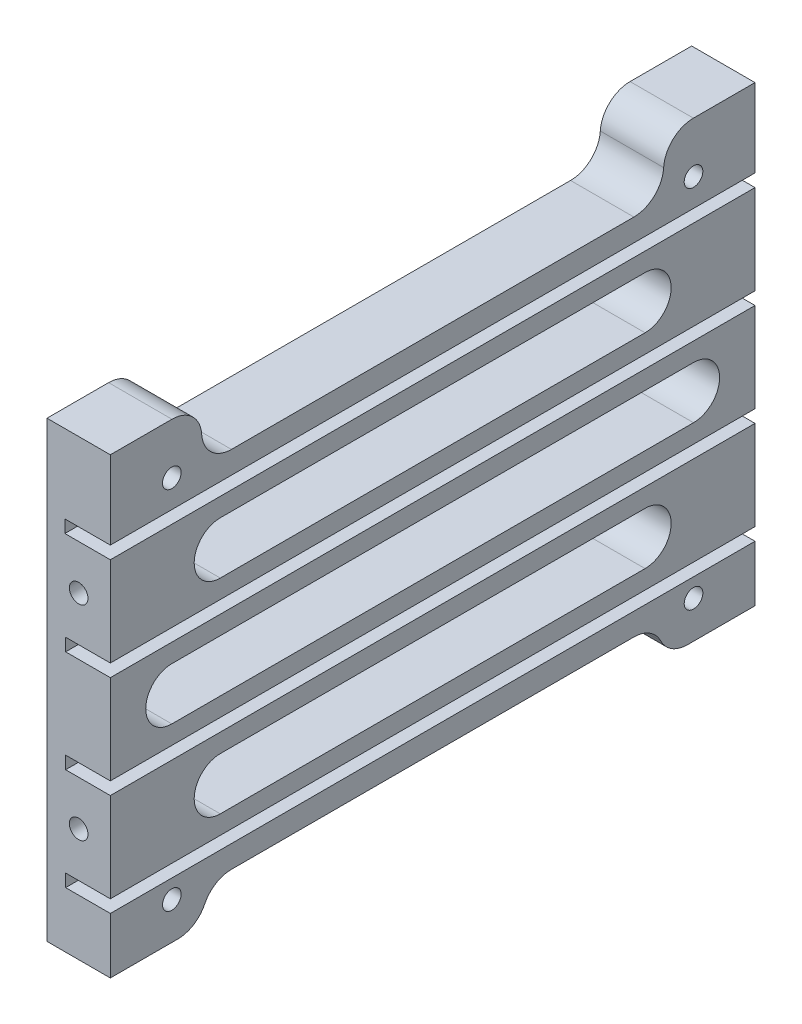
SolidWorks part; units mm, degrees
material "6061-T6 (SS)"
ref_plane "Front Plane" through (0, 0, 0) normal (0, 0, 1) x (1, 0, 0)
ref_plane "Top Plane" through (0, 0, 0) normal (0, 1, 0) x (1, 0, 0)
ref_plane "Right Plane" through (0, 0, 0) normal (1, 0, 0) x (0, 0, -1)
sketch "Sketch1" plane through (0, 0, 0) normal (0, 0, 1) x (1, 0, 0)
  line L0 (0, 0) -> (0, 60.8)
  line L1 (0, 60.8) -> (8.5, 60.8)
  line L2 (8.5, 60.8) -> (8.5, 50.3)
  line L3 (8.5, 50.3) -> (2.4, 50.3)
  line L4 (2.4, 50.3) -> (2.4, 48.6)
  line L5 (2.4, 48.6) -> (8.5, 48.6)
  line L6 (8.5, 48.6) -> (8.5, 36.6)
  line L7 (8.5, 36.6) -> (2.5, 36.6)
  line L8 (2.5, 36.6) -> (2.5, 34.9)
  line L9 (2.5, 34.9) -> (8.5, 34.9)
  line L10 (8.5, 34.9) -> (8.5, 22.9)
  line L11 (8.5, 22.9) -> (2.5, 22.9)
  line L12 (2.5, 22.9) -> (2.5, 21.2)
  line L13 (2.5, 21.2) -> (8.5, 21.2)
  line L14 (8.5, 21.2) -> (8.5, 9.2)
  line L15 (8.5, 9.2) -> (2.5, 9.2)
  line L16 (2.5, 9.2) -> (2.5, 7.5)
  line L17 (2.5, 7.5) -> (8.5, 7.5)
  line L18 (8.5, 7.5) -> (8.5, 0)
  line L19 (8.5, 0) -> (0, 0)
  dimension "D1" = 60.8
  dimension "D2" = 8.5
  dimension "D3" = 10.5
  dimension "D4" = 1.7
  dimension "D5" = 6.1
  dimension "D6" = 12
  dimension "D7" = 1.7
  dimension "D8" = 12
  dimension "D9" = 12
  dimension "D10" = 1.7
  dimension "D11" = 1.7
  dimension "D12" = 2.5
  dimension "D13" = 2.5
  dimension "D14" = 2.5
  dimension "D15" = 8.5
  dimension "D16" = 8.5
  dimension "D17" = 8.5
  dimension "D18" = 8.5
extrude "Boss-Extrude1" add sketch "Sketch1" along normal blind 86.5
sketch "Sketch2" plane through (0, 0, 86.5) normal (0, 0, 1) x (1, 0, 0)
  line L0 (8.5, 36.6) -> (8.5, 48.6) construction
  line L3 (8.5, 48.6) -> (2.4, 48.6) construction
  line L4 (8.5, 21.2) -> (2.5, 21.2) construction
  line L8 (8.5, 9.2) -> (8.5, 21.2) construction
  point P0 (4.25, 15.2)
  point P11 (4.25, 42.6)
  dimension "D1" = 4.25
  dimension "D2" = 6
  dimension "D3" = 4.25
  dimension "D4" = 6
hole_wizard "M3x0.5 Tapped Hole2" positions "Sketch3" profile "Sketch4" tap size "M3x0.5" standard "ANSI Metric"
sketch "Sketch3" plane through (0, 0, 86.5) normal (0, 0, 1) x (1, 0, 0)
  point P0 (4.25, 42.6)
  point P3 (4.25, 15.2)
sketch "Sketch4" plane through (4.25, 42.6, 86.5) normal (1, 0, 0) x (0, -1, 0)
  line L0 (0, 0) -> (0, 6.7511)
  line L1 (0, 6.7511) -> (1.25, 6)
  line L2 (1.25, 6) -> (1.25, 0)
  line L5 (1.25, 0) -> (0, 0)
  line L10 (0, 6.7511) -> (-1.25, 6) construction
  line L11 (0, -6.35) -> (0, 107.95) construction
  dimension "Tap Drill Dia." = 2.5
  dimension "Tap Drill Depth" = 6
  dimension "Drill Angle" = 118
ref_plane "Plane1" through (0, 0, 43.25) normal (0, 0, 1) x (1, 0, 0)
mirror "Mirror1" about plane through (0, 0, 43.25) normal (0, 0, 1) of "M3x0.5 Tapped Hole2"
sketch "Sketch5" plane through (0, 0, 0) normal (-1, 0, 0) x (0, 0, 1)
  line L1 (86.5, 60.8) -> (0, 60.8) construction
  line L5 (0, 60.8) -> (0, 0) construction
  line L7 (86.5, 0) -> (0, 0) construction
  line L8 (86.5, 60.8) -> (86.5, 0) construction
  point P0 (78.25, 5)
  point P3 (8.25, 5)
  point P4 (8.25, 55.8)
  point P7 (78.25, 55.8)
  dimension "D1" = 5
  dimension "D2" = 8.25
  dimension "D3" = 70
  dimension "D4" = 5
  dimension "D5" = 5
  dimension "D6" = 8.25
  dimension "D7" = 8.25
  dimension "D8" = 5
hole_wizard "M3x0.5 Tapped Hole1" positions "Sketch10" profile "Sketch11" tap size "M3x0.5" standard "ANSI Metric" end condition through all
sketch "Sketch10" plane through (0, 0, 0) normal (-1, 0, 0) x (0, 0, 1)
  line L0 (43.25, 60.8) -> (43.25, 0) construction
  line L1 (86.5, 60.8) -> (0, 60.8) construction
  line L2 (86.5, 0) -> (0, 0) construction
  line L7 (43.25, 54) -> (8.25, 54) construction
  line L12 (43.25, 5) -> (8.25, 5) construction
  point P16 (8.25, 54)
  point P26 (8.25, 5)
  dimension "D1" = 49
sketch "Sketch11" plane through (0, 5, 8.25) normal (0, 1, 0) x (0, 0, 1)
  line L0 (0, 0) -> (0, 8.5)
  line L1 (0, 8.5) -> (1.25, 8.5)
  line L2 (1.25, 8.5) -> (1.25, 0)
  line L5 (1.25, 0) -> (0, 0)
  line L11 (0, -6.35) -> (0, 107.95) construction
  dimension "Thru Tap Drill Dia." = 2.5
  dimension "Thru Tap Drill Depth" = 8.5
ref_plane "Plane2" through (0, 0, 43.25) normal (0, 0, -1) x (-1, 0, 0)
mirror "Mirror2" about plane through (0, 0, 43.25) normal (0, 0, -1) of "M3x0.5 Tapped Hole1"
sketch "Sketch14" plane through (8.5, 0, 0) normal (1, 0, 0) x (0, 0, -1)
  line L0 (-43.25, 60.8) -> (-43.25, 0) construction
  line L1 (-86.5, 60.8) -> (0, 60.8) construction
  line L2 (-86.5, 0) -> (0, 0) construction
  line L3 (-86.5, 28.9) -> (0, 28.9) construction
  line L4 (-86.5, 22.9) -> (-86.5, 34.9) construction
  line L5 (0, 22.9) -> (0, 34.9) construction
  line L6 (-78.25, 32.4) -> (-8.25, 32.4)
  line L7 (-8.25, 25.4) -> (-78.25, 25.4)
  circle A0 centre (-78.25, 28.9) radius 3.5
  circle A1 centre (-8.25, 28.9) radius 3.5
  dimension "D1" = 7
  dimension "D2" = 35
extrude "Cut-Extrude3" cut sketch "Sketch14" against normal through all contours A1 L6 A0 L7 | A0 | A1
sketch "Sketch12" plane through (8.5, 0, 0) normal (1, 0, 0) x (0, 0, -1)
  line L0 (-43.25, 60.8) -> (-43.25, 0) construction
  line L1 (-86.5, 60.8) -> (0, 60.8) construction
  line L2 (-86.5, 0) -> (0, 0) construction
  line L3 (-86.5, 21.2) -> (0, 21.2) construction
  line L4 (-71.75, 46.1) -> (-14.75, 46.1)
  line L5 (-71.75, 39.1) -> (-14.75, 39.1)
  line L6 (-71.75, 18.7) -> (-14.75, 18.7)
  line L7 (-71.75, 11.7) -> (-14.75, 11.7)
  line L9 (-86.5, 48.6) -> (0, 48.6) construction
  circle A0 centre (-71.75, 42.6) radius 3.5
  circle A1 centre (-14.75, 42.6) radius 3.5
  circle A2 centre (-14.75, 15.2) radius 3.5
  circle A3 centre (-71.75, 15.2) radius 3.5
  dimension "D1" = 7
  dimension "D2" = 28.5
  dimension "D3" = 2.5
  dimension "D4" = 2.5
extrude "Cut-Extrude1" cut sketch "Sketch12" against normal through all contours A0 | A3 | A2 | A1 | L0 L6 A3 L7 | L6 L0 L7 A2 | L4 L0 L5 A1 | L0 L4 A0 L5
sketch "Sketch15" plane through (8.5, 0, 0) normal (1, 0, 0) x (0, 0, -1)
  line L0 (-86.5, 60.8) -> (0, 60.8) construction
  line L1 (-74.25, 60.8) -> (-12.25, 60.8)
  line L2 (-74.25, 60.8) -> (-74.25, 53.3)
  line L3 (-74.25, 53.3) -> (-12.25, 53.3)
  line L4 (-12.25, 60.8) -> (-12.25, 53.3)
  line L5 (-74.25, 60.8) -> (-12.25, 53.3) construction
  line L6 (-74.25, 53.3) -> (-12.25, 60.8) construction
  point P0 (-43.25, 57.05)
  point P7 (-43.25, 60.8)
  dimension "D1" = 62
  dimension "D2" = 7.5
extrude "Cut-Extrude4" cut sketch "Sketch15" against normal through all contours L2 L3 L4 L1
sketch "Sketch16" plane through (8.5, 0, 0) normal (1, 0, 0) x (0, 0, -1)
  line L0 (-86.5, 0) -> (0, 0) construction
  line L1 (-74.25, 4.5) -> (-12.25, 4.5)
  line L2 (-74.25, 4.5) -> (-74.25, 0)
  line L3 (-74.25, 0) -> (-12.25, 0)
  line L4 (-12.25, 4.5) -> (-12.25, 0)
  line L5 (-74.25, 4.5) -> (-12.25, 0) construction
  line L6 (-74.25, 0) -> (-12.25, 4.5) construction
  point P0 (-43.25, 2.25)
  point P8 (-43.25, 0)
  dimension "D1" = 4.5
  dimension "D2" = 62
extrude "Cut-Extrude5" cut sketch "Sketch16" against normal through all
fillet "Fillet2" radius 4 4 edges at (4.25, 4.5, 74.25) (4.25, 4.5, 12.25) (4.25, 53.3, 12.25) (4.25, 53.3, 74.25)
fillet "Fillet3" radius 4 4 edges at (4.25, 0, 12.25) (4.25, 0, 74.25) (4.25, 60.8, 12.25) (4.25, 60.8, 74.25)
